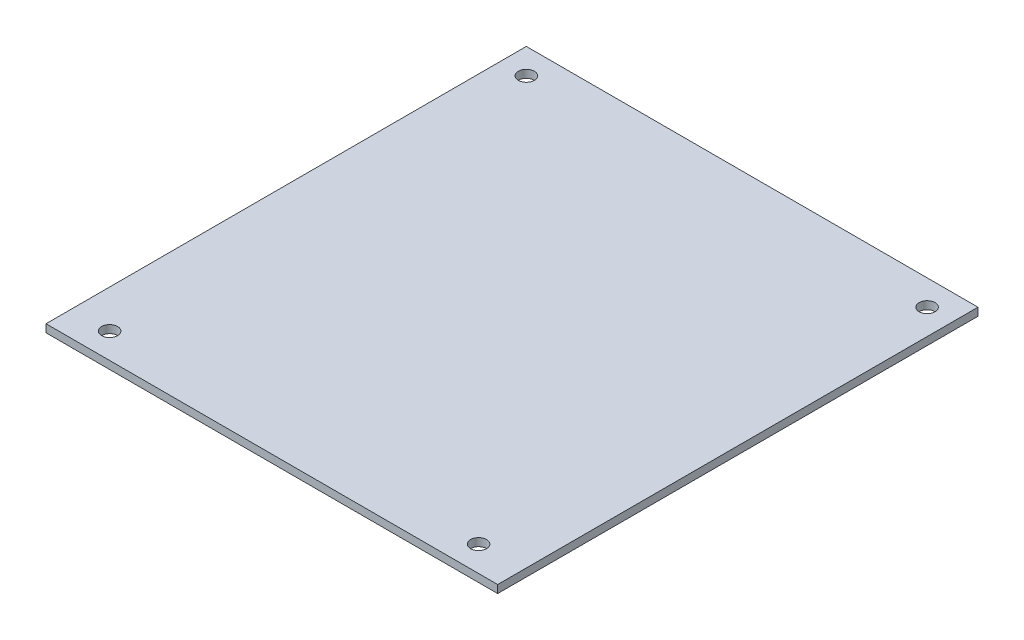
SolidWorks part; units mm, degrees
ref_plane "Front Plane" through (0, 0, 0) normal (0, 0, 1) x (1, 0, 0)
ref_plane "Top Plane" through (0, 0, 0) normal (0, 1, 0) x (1, 0, 0)
ref_plane "Right Plane" through (0, 0, 0) normal (1, 0, 0) x (0, 0, -1)
sketch "Sketch1" plane through (0, 0, 0) normal (0, 1, 0) x (1, 0, 0)
  line L0 (0, -47.945) -> (0, 47.945) construction
  point P0 (0, 47.945)
  point P1 (0, -47.945)
  point P5 (0, 0)
  line B0 (31.62, -34.735) -> (31.62, -46.035)
  line B1 (-31.73, -34.735) -> (31.62, -34.735)
  line B2 (31.62, -46.035) -> (-31.73, -46.035)
  line B3 (-31.73, -46.035) -> (-31.73, -34.735)
  line B4 (40.255, 34.355) -> (40.255, 39.305)
  line B5 (-41.535, 34.355) -> (40.255, 34.355)
  line B6 (-41.535, 39.305) -> (-41.535, 34.355)
  line B7 (-31.375, 39.305) -> (-41.535, 39.305)
  line B8 (-31.375, 44.385) -> (-31.375, 39.305)
  line B9 (19.935, 44.385) -> (-31.375, 44.385)
  line B10 (19.935, 39.305) -> (19.935, 44.385)
  line B11 (40.255, 39.305) -> (19.935, 39.305)
  line B12 (-45.085, -47.945) -> (45.085, -47.945)
  line B13 (45.085, -47.945) -> (45.085, 47.945)
  line B14 (45.085, 47.945) -> (-45.085, 47.945)
  line B15 (-45.085, 47.945) -> (-45.085, -47.945)
  circle B16 centre (-40.005, 42.865) radius 1.59
  circle B17 centre (-37.465, -42.865) radius 1.59
  circle B18 centre (36.195, -42.865) radius 1.59
  circle B19 centre (40.005, 42.865) radius 1.59
sketch_block_instance "Block-PC104 Block-1"
sketch_block "Block-PC104 Block"
extrude "Boss-Extrude1" add sketch "Sketch1" along normal mid plane 1.57 contours B12 L0 B2 B3 B1 B5 B6 B7 B8 B9 B14 B15 B16 B17 | L0 B12 B13 B14 B9 B10 B11 B4 B5 B1 B0 B2 B19 B18 | L0 B2 B0 B1 | B2 L0 B1 B3 | B5 L0 B9 B8 B7 B6 | L0 B5 B4 B11 B10 B9
